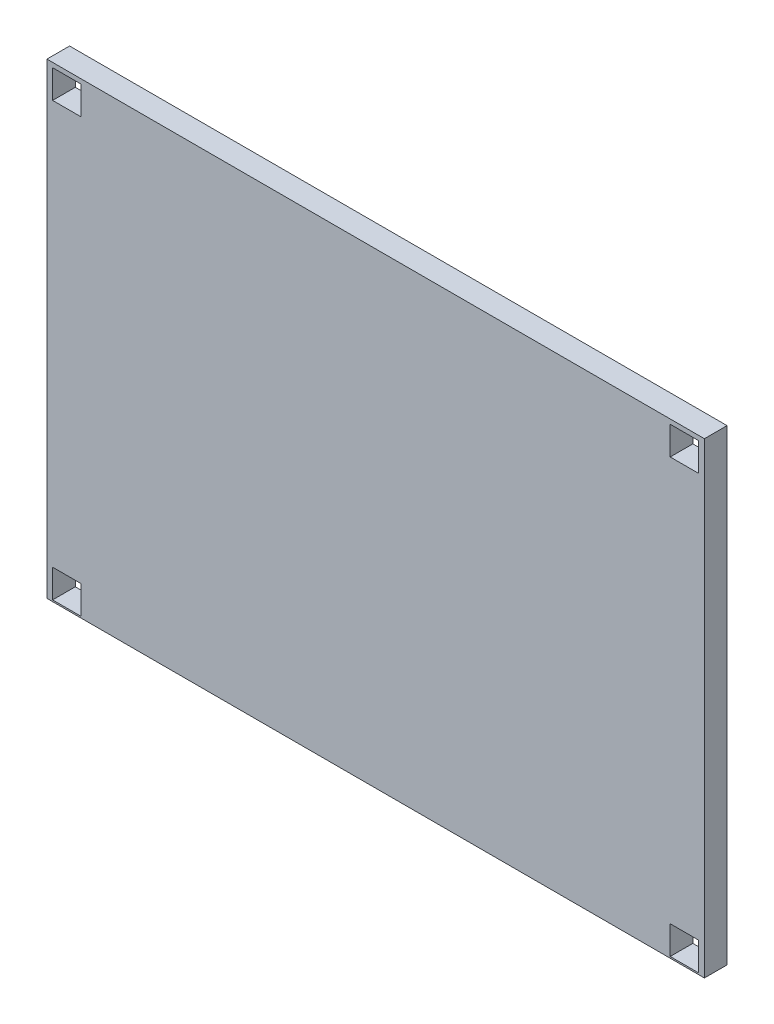
SolidWorks part; units mm, degrees
material "Balsa"
ref_plane "Front Plane" through (0, 0, 0) normal (0, 0, 1) x (1, 0, 0)
ref_plane "Top Plane" through (0, 0, 0) normal (0, 1, 0) x (1, 0, 0)
ref_plane "Right Plane" through (0, 0, 0) normal (1, 0, 0) x (0, 0, -1)
sketch "Sketch2" plane through (0, 0, 0) normal (0, 0, 1) x (1, 0, 0)
  line L0 (44.1654, 130.5904) -> (44.1654, 25.9424)
  line L5 (191.4854, 130.5904) -> (191.4854, 25.9424)
  line L6 (44.1654, 130.5904) -> (191.4854, 130.5904)
  line L7 (44.1654, 25.9424) -> (191.4854, 25.9424)
extrude "Boss-Extrude1" add sketch "Sketch2" along normal blind 5.08
sketch "Sketch3" plane through (0, 0, 0) normal (0, 0, 1) x (1, 0, 0)
  circle A0 centre (69.5996, 110.562) radius 19.05
  circle A1 centre (69.5996, 45.6226) radius 19.05
  circle A2 centre (92.5808, 77.8311) radius 19.05
  circle A3 centre (115.5621, 110.562) radius 19.05
  circle A4 centre (115.5621, 45.6226) radius 19.05
  circle A5 centre (140.2844, 77.8311) radius 19.05
  circle A6 centre (165.8771, 110.562) radius 19.05
  circle A7 centre (165.8771, 45.6226) radius 19.05
extrude "Cut-Extrude1" cut sketch "Sketch3" along normal blind 2.54
sketch "Sketch4" plane through (0, 0, 0) normal (0, 0, 1) x (1, 0, 0)
  circle A0 centre (69.5996, 45.6226) radius 12.7
  circle A1 centre (115.5621, 45.6226) radius 12.7
  circle A2 centre (165.8771, 45.6226) radius 12.7
  circle A3 centre (92.5808, 77.8311) radius 12.7
  circle A4 centre (140.2844, 77.8311) radius 12.7
  circle A5 centre (69.5996, 110.562) radius 12.7
  circle A6 centre (115.5621, 110.562) radius 12.7
  circle A7 centre (165.8771, 110.562) radius 12.7
extrude "Cut-Extrude2" cut sketch "Sketch4" along normal blind 3.81
sketch "Sketch5" plane through (0, 0, 0) normal (0, 0, 1) x (1, 0, 0)
  line L1 (45.4404, 26.2866) -> (51.7904, 26.2866)
  line L2 (45.4404, 26.2866) -> (45.4404, 32.6366)
  line L3 (45.4404, 32.6366) -> (51.7904, 32.6366)
  line L4 (51.7904, 26.2866) -> (51.7904, 32.6366)
  line L5 (190.1692, 26.2866) -> (183.8192, 26.2866)
  line L6 (190.1692, 26.2866) -> (190.1692, 32.6366)
  line L7 (190.1692, 32.6366) -> (183.8192, 32.6366)
  line L8 (183.8192, 26.2866) -> (183.8192, 32.6366)
  line L9 (190.1692, 129.561) -> (183.8192, 129.561)
  line L10 (190.1692, 129.561) -> (190.1692, 123.211)
  line L11 (190.1692, 123.211) -> (183.8192, 123.211)
  line L12 (183.8192, 129.561) -> (183.8192, 123.211)
  line L13 (45.4404, 129.561) -> (51.7904, 129.561)
  line L14 (45.4404, 129.561) -> (45.4404, 123.211)
  line L15 (45.4404, 123.211) -> (51.7904, 123.211)
  line L16 (51.7904, 129.561) -> (51.7904, 123.211)
extrude "Cut-Extrude3" cut sketch "Sketch5" along normal blind 6.35
